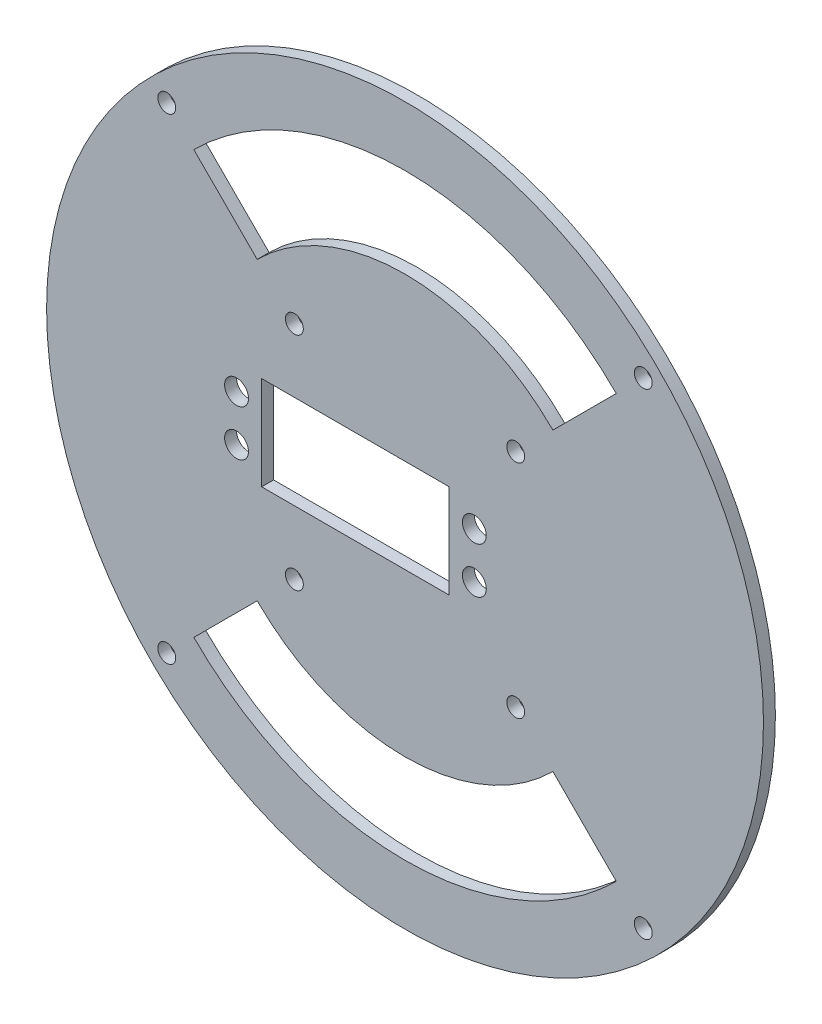
SolidWorks part; units mm, degrees
ref_plane "Front Plane" through (0, 0, 0) normal (0, 0, 1) x (1, 0, 0)
ref_plane "Top Plane" through (0, 0, 0) normal (0, 1, 0) x (1, 0, 0)
ref_plane "Right Plane" through (0, 0, 0) normal (1, 0, 0) x (0, 0, -1)
sketch "Sketch1" plane through (0, 0, 0) normal (0, 0, 1) x (1, 0, 0)
  line L0 (0, 0) -> (35355.3391, 35355.3391) construction
  line L1 (-30.48, -9.9695) -> (9.398, -9.9695)
  line L2 (-30.48, -9.9695) -> (-30.48, 9.9695)
  line L3 (-30.48, 9.9695) -> (9.398, 9.9695)
  line L4 (9.398, -9.9695) -> (9.398, 9.9695)
  line L5 (0, 0) -> (35355.3391, -35355.3391) construction
  line L6 (-44.9013, -44.9013) -> (-31.4309, -31.4309)
  line L7 (31.4309, -31.4309) -> (44.9013, -44.9013)
  line L8 (44.9013, 44.9013) -> (31.4309, 31.4309)
  line L9 (-31.4309, 31.4309) -> (-44.9013, 44.9013)
  line L10 (50.6486, 50.6486) -> (53.8815, 53.8815) construction
  circle A0 centre (0, 0) radius 76.2
  circle A1 centre (0, 0) radius 3.175 construction
  circle A2 centre (0, 0) radius 63.5 construction
  circle A3 centre (0, 0) radius 44.45 construction
  circle A4 centre (14.732, -4.8895) radius 2.54
  circle A5 centre (14.732, 4.8895) radius 2.54
  circle A6 centre (-35.814, 4.8895) radius 2.54
  circle A7 centre (-35.814, -4.8895) radius 2.54
  arc A8 (-31.4309, -31.4309) -> (31.4309, -31.4309) centre (0, 0) ccw
  arc A9 (44.9013, -44.9013) -> (-44.9013, -44.9013) centre (0, 0) cw
  arc A10 (31.4309, 31.4309) -> (-31.4309, 31.4309) centre (0, 0) ccw
  arc A11 (-44.9013, 44.9013) -> (44.9013, 44.9013) centre (0, 0) cw
  circle A12 centre (23.5283, 23.5283) radius 1.905
  circle A13 centre (23.5283, -23.5283) radius 1.905
  circle A14 centre (-23.5283, -23.5283) radius 1.905
  circle A15 centre (-23.5283, 23.5283) radius 1.905
  circle A16 centre (50.6486, 50.6486) radius 1.905
  circle A17 centre (50.6486, -50.6486) radius 1.905
  circle A18 centre (-50.6486, -50.6486) radius 1.905
  circle A19 centre (-50.6486, 50.6486) radius 1.905
  point P36 (0, 0)
  point P45 (0, 0)
  point P54 (0, 0)
  dimension "D1" = 39.878
  dimension "D3" = 30.48
  dimension "D4" = 6.35
  dimension "D6" = 0
  dimension "D8" = 5.334
  dimension "D10" = 5.08
  dimension "D11" = 5.334
  dimension "D12" = 2
  dimension "D13" = 33.274
  dimension "D15" = 4.572
  dimension "D2" = 19.939
  dimension "D5" = 9.9695
  dimension "D7" = 0
  dimension "D9" = 5.08
  dimension "D14" = 4
  dimension "D16" = 4
extrude "Boss-Extrude1" add sketch "Sketch1" along normal blind 2.54
